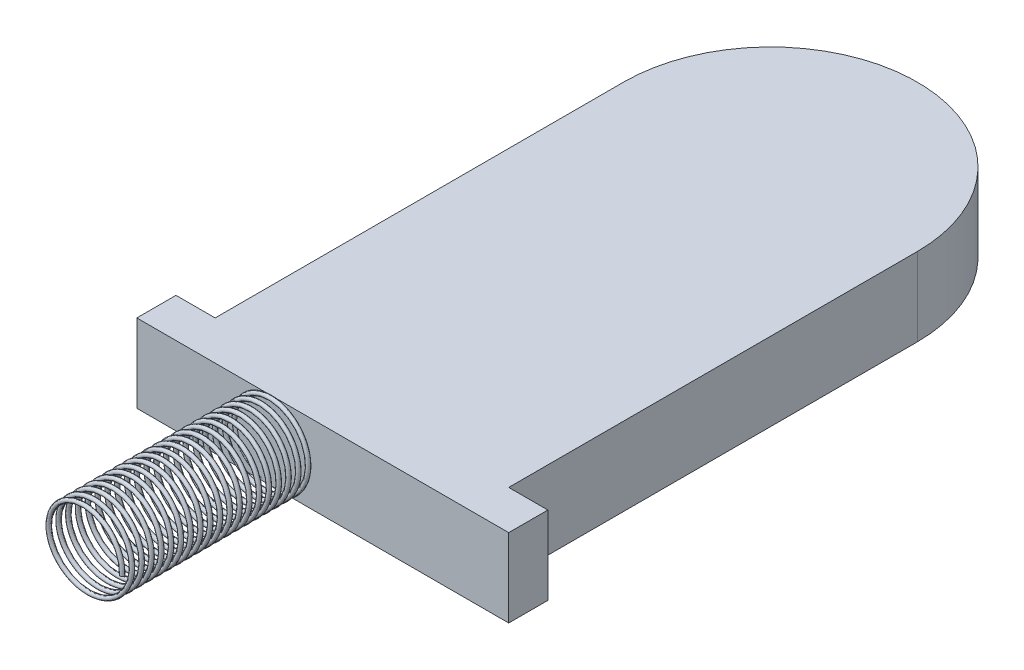
SolidWorks part; units mm, degrees
ref_plane "前视基准面" through (0, 0, 0) normal (0, 0, 1) x (1, 0, 0)
ref_plane "上视基准面" through (0, 0, 0) normal (0, 1, 0) x (1, 0, 0)
ref_plane "右视基准面" through (0, 0, 0) normal (1, 0, 0) x (0, 0, -1)
sketch "草图1" plane through (0, 0, 0) normal (0, 1, 0) x (1, 0, 0)
  line L1 (-0.5, -1.0875) -> (-0.7, -1.0875)
  line L2 (-0.5, 1) -> (-0.5, -1.0875)
  line L3 (1.2, -1.2875) -> (-0.7, -1.2875)
  line L4 (1, 1) -> (1, -1.0875)
  line L8 (1.2, -1.2875) -> (1.2, -1.0875)
  line L9 (1.2, -1.0875) -> (1, -1.0875)
  line L10 (-0.7, -1.0875) -> (-0.7, -1.2875)
  arc A1 (1, 1) -> (-0.5, 1) centre (0.25, 1) ccw
  point P0 (0, 0)
  dimension "D1" = 0.2
  dimension "D2" = 0.2
  dimension "D3" = 0.2
  dimension "D4" = 1.5
extrude "凸台-拉伸1" add sketch "草图1" along normal blind 0.4
sketch "草图2" plane through (0, 0, 1.2875) normal (0, 0, 1) x (1, 0, 0)
  circle A0 centre (0, 0.2) radius 0.2
curve "螺旋线/涡状线1" pitch 0.05 height 1 turns 20
sketch "草图3" plane through (0, 0, 1.2875) normal (0, 0, 1) x (1, 0, 0)
  line L0 (-0.7, 0.2) -> (1.2, 0.2)
  line L1 (-0.7, 0.4) -> (-0.7, 0) construction
  line L2 (1.2, 0.4) -> (1.2, 0) construction
ref_plane "基准面1" through (0, 0.2, 0) normal (0, -1, 0) x (1, 0, 0)
sketch "草图4" plane through (0, 0.2, 0) normal (0, -1, 0) x (1, 0, 0)
  line L1 (-0.7, 1.2875) -> (1.2, 1.2875) construction
  circle A0 centre (-0.2, 1.2875) radius 0.01
sweep "扫描1" add profiles "草图4" path "螺旋线/涡状线1"
